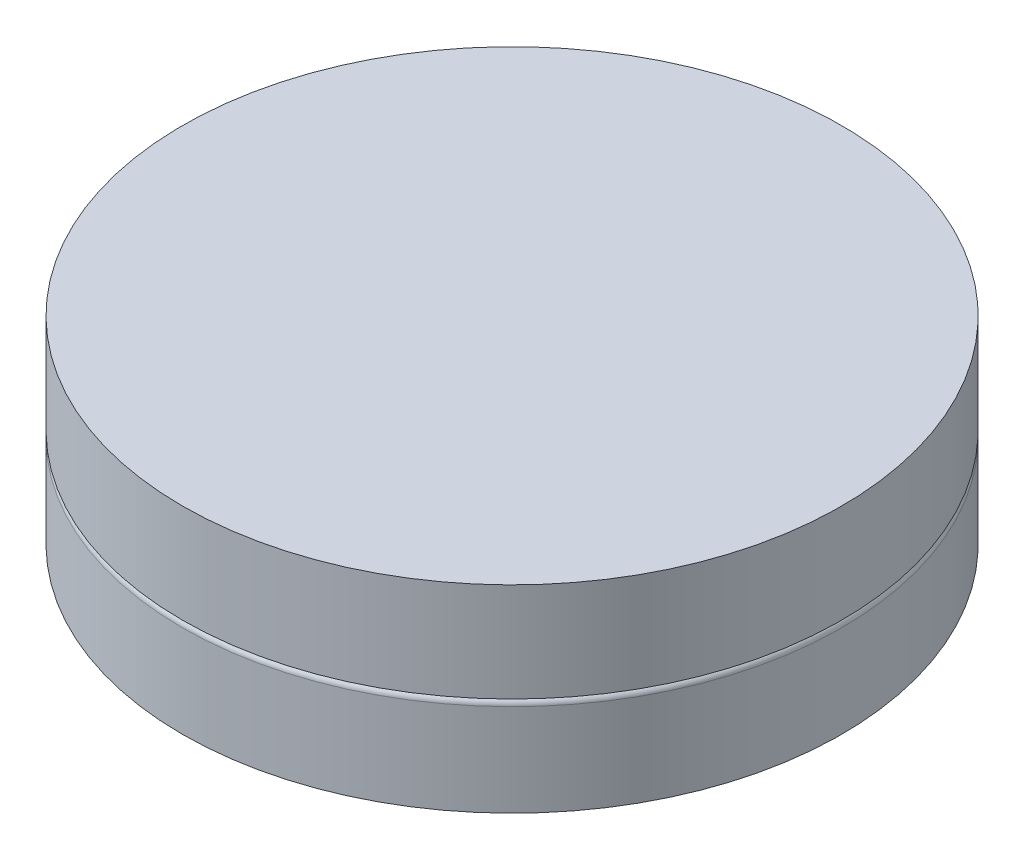
SolidWorks part; units mm, degrees
ref_plane "Front Plane" through (0, 0, 0) normal (0, 0, 1) x (1, 0, 0)
ref_plane "Top Plane" through (0, 0, 0) normal (0, 1, 0) x (1, 0, 0)
ref_plane "Right Plane" through (0, 0, 0) normal (1, 0, 0) x (0, 0, -1)
sketch "Sketch1" plane through (0, 0, 0) normal (0, 1, 0) x (1, 0, 0)
  circle A0 centre (0, 0) radius 2.5
  dimension "D1" = 5
extrude "Boss-Extrude1" add sketch "Sketch1" along normal blind 0.75
fillet "Fillet1" radius 0.05 1 edges at (0, 0.75, 2.5)
sketch "Sketch2" plane through (0, 0.75, 0) normal (0, 1, 0) x (1, 0, 0)
  circle A0 centre (0, 0) radius 2.5 construction
  circle A1 centre (0, 0) radius 2.5
extrude "Boss-Extrude2" add sketch "Sketch2" along normal blind 0.75
